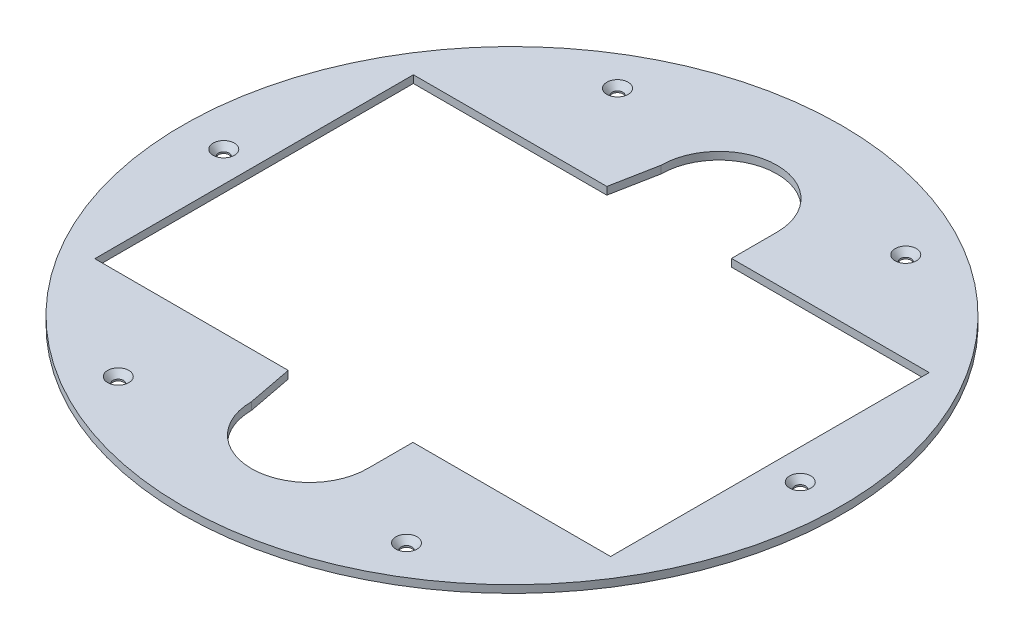
SolidWorks part; units mm, degrees
ref_plane "Front Plane" through (0, 0, 0) normal (0, 0, 1) x (1, 0, 0)
ref_plane "Top Plane" through (0, 0, 0) normal (0, 1, 0) x (1, 0, 0)
ref_plane "Right Plane" through (0, 0, 0) normal (1, 0, 0) x (0, 0, -1)
sketch "Sketch1" plane through (0, 0, 0) normal (0, 1, 0) x (1, 0, 0)
  line L1 (-107.95, -63.5) -> (107.95, -63.5) construction
  line L2 (-107.95, -63.5) -> (-107.95, 63.5) construction
  line L3 (-107.95, 63.5) -> (107.95, 63.5) construction
  line L4 (107.95, -63.5) -> (107.95, 63.5) construction
  line L5 (-107.95, -63.5) -> (107.95, 63.5) construction
  line L6 (-107.95, 63.5) -> (107.95, -63.5) construction
  circle A0 centre (0, 0) radius 125.2416 construction
  circle A1 centre (0, 0) radius 137.9416
  point P0 (0, 0)
  dimension "D3" = 12.7
  dimension "D1" = 215.9
  dimension "D2" = 127
extrude "Extrude1" add sketch "Sketch1" along normal blind 3.175
sketch "Sketch3" plane through (0, 3.175, 0) normal (0, 1, 0) x (1, 0, 0)
  line L0 (25.2049, -66.675) -> (107.95, -66.675)
  line L1 (-107.95, -66.675) -> (-26.9875, -66.675)
  line L2 (-107.95, -66.675) -> (-107.95, 66.675)
  line L3 (-107.95, 66.675) -> (-26.9875, 66.675)
  line L4 (107.95, -66.675) -> (107.95, 66.675)
  line L5 (-107.95, -66.675) -> (107.95, 66.675) construction
  line L6 (-107.95, 66.675) -> (107.95, -66.675) construction
  line L7 (25.2049, 66.675) -> (107.95, 66.675)
  line L8 (0, 93.6625) -> (0, -93.6625) construction
  line L9 (25.2049, -85.725) -> (25.2049, -66.675)
  line L10 (-23.3298, -85.725) -> (-26.9875, -66.675)
  line L11 (0, 0) -> (-74.6519, 0) construction
  line L12 (-23.3298, 85.725) -> (-26.9875, 66.675)
  line L13 (25.2049, 85.725) -> (25.2049, 66.675)
  arc A1 (-23.3298, -85.725) -> (25.2049, -85.725) centre (0.9376, -85.725) ccw
  arc A2 (-23.3298, 85.725) -> (25.2049, 85.725) centre (0.9376, 85.725) cw
  point P0 (0, 0)
  dimension "D1" = 215.9
  dimension "D2" = 133.35
  dimension "D4" = 26.9875
extrude "Extrude3" cut sketch "Sketch3" against normal through all
sketch "Sketch4" plane through (0, 3.175, 0) normal (0, 1, 0) x (-1, 0, 0)
  line L0 (120.65, 0) -> (0, 0) construction
  circle A0 centre (120.65, 0) radius 1.5875
  dimension "D2" = 3.175
  dimension "D1" = 120.65
extrude "Extrude4" cut sketch "Sketch4" against normal through all
hole_wizard "CSK for #8 Flat Head Socket Cap Screw1" positions "3DSketch1" profile "Sketch5" countersink size "#8" standard "Ansi Inch" end condition through all
sketch3d "3DSketch1"
  line L0 (-120.65, 0, 0) -> (-120.65, 3.175, 0) construction
  point P0 (-120.65, 3.175, 0)
sketch "Sketch5" plane through (-120.65, 3.175, 0) normal (1, 0, 0) x (0, 0, 1)
  line L0 (0, 0) -> (0, 3.175)
  line L1 (0, 3.175) -> (2.2479, 3.175)
  line L2 (2.2479, 3.175) -> (2.2479, 2.5275)
  line L3 (2.2479, 2.5275) -> (4.445, 0)
  line L5 (4.445, 0) -> (0, 0)
  line L6 (-2.2479, 2.5275) -> (-4.445, 0) construction
  line L11 (0, -6.35) -> (0, 107.95) construction
  dimension "Thru Hole Dia." = 4.4958
  dimension "Thru Hole Depth" = 3.175
  dimension "Near C'Sink Dia." = 8.89
  dimension "Near C'Sink Angle" = 82
pattern_circular "CirPattern1" count 6 over 360 about axis through (0, 0, 0) along (0, 1, 0) of "CSK for #8 Flat Head Socket Cap Screw1"
